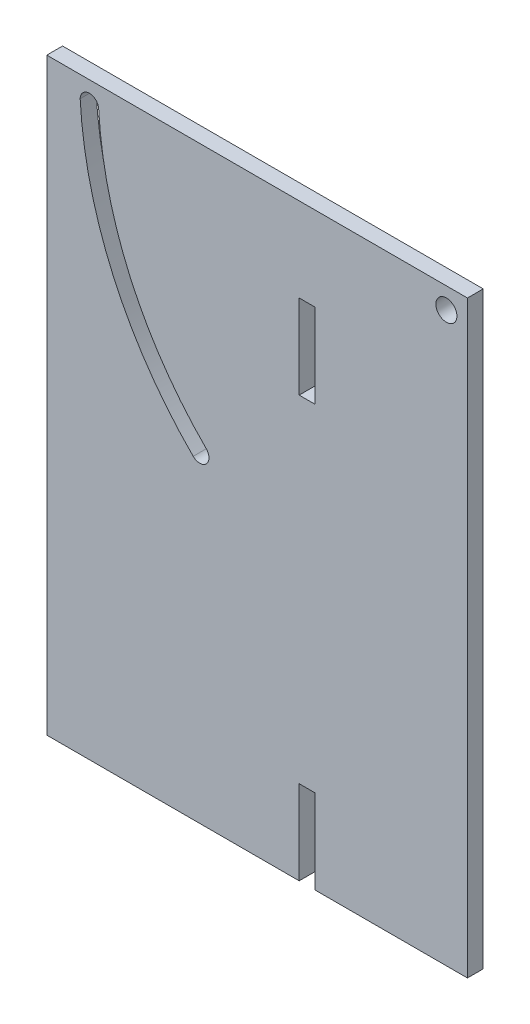
SolidWorks part; units mm, degrees
ref_plane "Front Plane" through (0, 0, 0) normal (0, 0, 1) x (1, 0, 0)
ref_plane "Top Plane" through (0, 0, 0) normal (0, 1, 0) x (1, 0, 0)
ref_plane "Right Plane" through (0, 0, 0) normal (1, 0, 0) x (0, 0, -1)
sketch "Sketch1" plane through (0, 0, 0) normal (0, 0, 1) x (1, 0, 0)
  line L0 (80.9625, 0) -> (127, 0)
  line L1 (0, 0) -> (76.2, 0)
  line L2 (0, 0) -> (0, 177.8)
  line L3 (0, 177.8) -> (127, 177.8)
  line L4 (127, 0) -> (127, 177.8)
  line L5 (76.2, 152.4) -> (80.9625, 152.4)
  line L6 (76.2, 152.4) -> (76.2, 127)
  line L7 (76.2, 127) -> (80.9625, 127)
  line L8 (80.9625, 152.4) -> (80.9625, 127)
  line L9 (76.2, 25.4) -> (80.9625, 25.4)
  line L10 (76.2, 25.4) -> (76.2, 0)
  line L12 (80.9625, 25.4) -> (80.9625, 0)
  arc A0 (10.0783, 171.45) -> (44.202, 95.002) centre (127, 177.8) ccw
  arc A1 (15.675, 171.45) -> (48.1534, 98.9534) centre (127, 177.8) ccw
  circle A2 centre (120.65, 171.45) radius 3.175
  arc A3 (15.675, 171.45) -> (10.0783, 171.45) centre (12.8766, 171.45) ccw
  arc A4 (48.1534, 98.9534) -> (44.202, 95.002) centre (46.1777, 96.9777) cw
  dimension "D2" = 177.8
  dimension "D4" = 127
extrude "Boss-Extrude1" add sketch "Sketch1" along normal blind 4.7625
